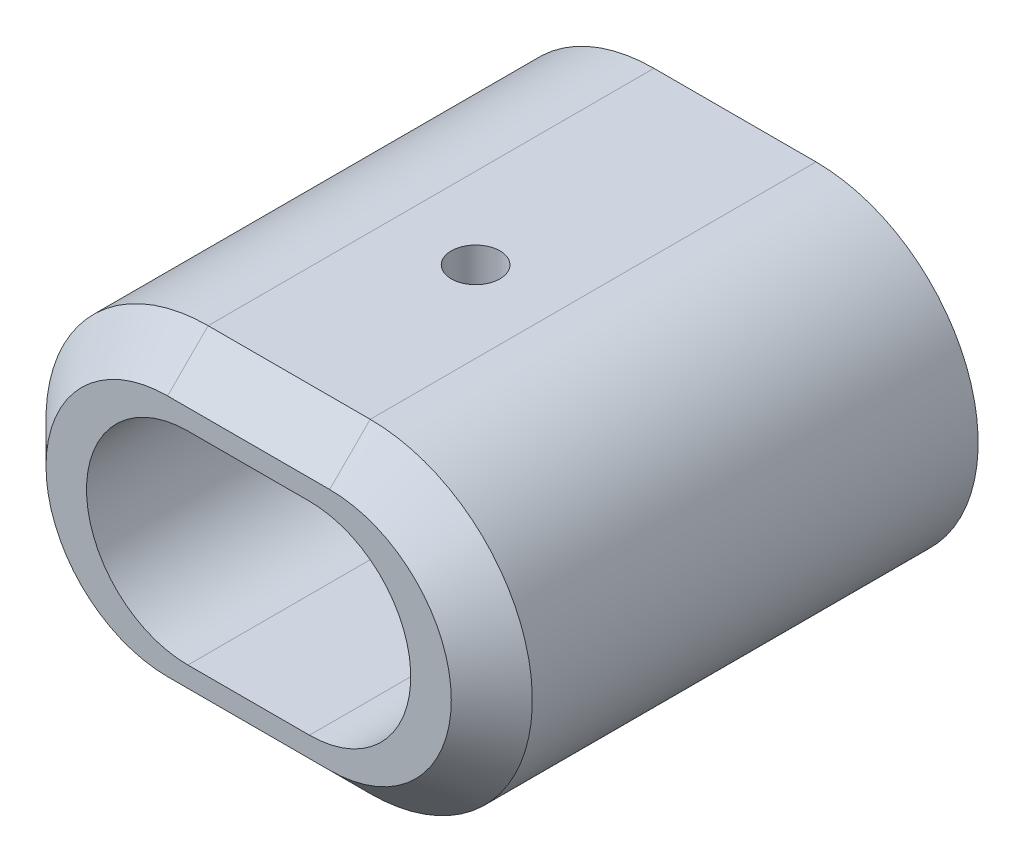
SolidWorks part; units mm, degrees
ref_plane "Front Plane" through (0, 0, 0) normal (0, 0, 1) x (1, 0, 0)
ref_plane "Top Plane" through (0, 0, 0) normal (0, 1, 0) x (1, 0, 0)
ref_plane "Right Plane" through (0, 0, 0) normal (1, 0, 0) x (0, 0, -1)
sketch "Sketch1" plane through (0, 0, 0) normal (0, 0, 1) x (1, 0, 0)
  line L0 (-7.5, 0) -> (7.5, 0) construction
  line L1 (-7.5, 12.5) -> (7.5, 12.5)
  line L2 (-7.5, -12.5) -> (7.5, -12.5)
  line L3 (-10, 0) -> (10, 0) construction
  line L4 (-10, 20) -> (10, 20)
  line L5 (-10, -20) -> (10, -20)
  arc A0 (-7.5, 12.5) -> (-7.5, -12.5) centre (-7.5, 0) ccw
  arc A1 (7.5, -12.5) -> (7.5, 12.5) centre (7.5, 0) ccw
  arc A2 (-10, 20) -> (-10, -20) centre (-10, 0) ccw
  arc A3 (10, -20) -> (10, 20) centre (10, 0) ccw
  point P2 (0, 0)
  point P10 (0, 0)
  point P15 (-30, 0)
  point P16 (30, 0)
  dimension "D1" = 25
  dimension "D2" = 15
  dimension "D3" = 40
  dimension "D4" = 60
extrude "Boss-Extrude1" add sketch "Sketch1" along normal blind 60
sketch "Sketch4" plane through (0, -20, 0) normal (0, -1, 0) x (1, 0, 0)
  line L0 (10, 60) -> (-10, 60) construction
  circle A0 centre (0, 32) radius 3
  point P2 (0, 60)
  dimension "D2" = 6
  dimension "D1" = 28
extrude "Cut-Extrude1" cut sketch "Sketch4" against normal blind 60
chamfer "Chamfer1" distance 5 angle 45 4 edges at (0, 20, 60) (30, 0, 60) (0, -20, 60) (-30, 0, 60)
